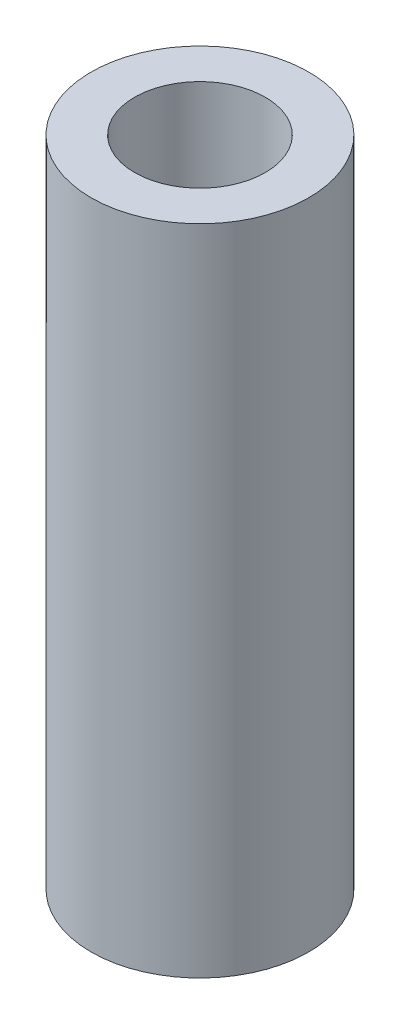
SolidWorks part; units mm, degrees
ref_plane "Front Plane" through (0, 0, 0) normal (0, 0, 1) x (1, 0, 0)
ref_plane "Top Plane" through (0, 0, 0) normal (0, 1, 0) x (1, 0, 0)
ref_plane "Right Plane" through (0, 0, 0) normal (1, 0, 0) x (0, 0, -1)
sketch "Sketch1" plane through (0, 0, 0) normal (0, 1, 0) x (1, 0, 0)
  circle A0 centre (0, 0) radius 2.5
  circle A1 centre (0, 0) radius 1.5
  dimension "D1" = 5
  dimension "D2" = 3
extrude "Boss-Extrude1" add sketch "Sketch1" along normal blind 15
